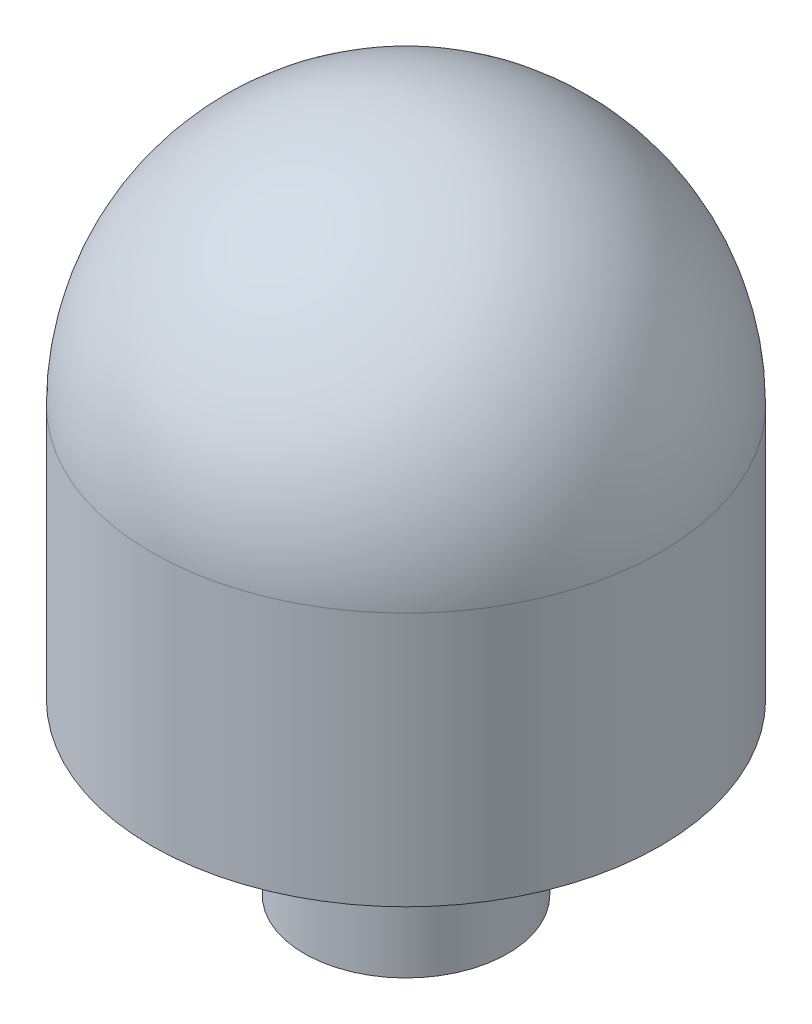
SolidWorks part; units mm, degrees
ref_plane "Alzado" through (0, 0, 0) normal (0, 0, 1) x (1, 0, 0)
ref_plane "Planta" through (0, 0, 0) normal (0, 1, 0) x (1, 0, 0)
ref_plane "Vista lateral" through (0, 0, 0) normal (1, 0, 0) x (0, 0, -1)
sketch "Croquis1" plane through (0, 0, 0) normal (0, 0, 1) x (1, 0, 0)
  line L0 (0, 0) -> (-6, 0)
  line L1 (-6, 0) -> (-6, 10)
  line L2 (-6, 10) -> (-15, 10)
  line L3 (-15, 10) -> (-15, 25)
  line L4 (0, 40) -> (0, 0)
  arc A0 (-15, 25) -> (0, 40) centre (0, 25) cw
  dimension "D1" = 15
  dimension "D2" = 25
  dimension "D3" = 10
  dimension "D4" = 6
  dimension "D5" = 15
revolve "Revolución1" add sketch "Croquis1" angle 360 about L4
